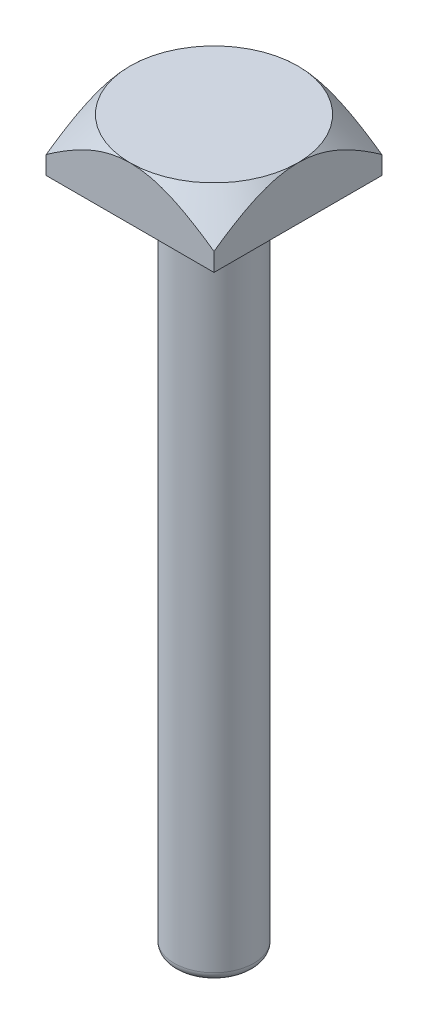
SolidWorks part; units mm, degrees
ref_plane "Front Plane" through (0, 0, 0) normal (0, 0, 1) x (1, 0, 0)
ref_plane "Top Plane" through (0, 0, 0) normal (0, 1, 0) x (1, 0, 0)
ref_plane "Right Plane" through (0, 0, 0) normal (1, 0, 0) x (0, 0, -1)
sketch "Sketch1" plane through (0, 0, 0) normal (0, 0, 1) x (1, 0, 0)
  line L1 (0, 0) -> (4.5, 0)
  line L2 (0, 0) -> (0, -76)
  line L3 (0, -76) -> (4.5, -76)
  line L4 (4.5, 0) -> (4.5, -76)
  dimension "D1" = 76
  dimension "D2" = 4.5
revolve "Revolve1" add sketch "Sketch1" angle 360 about L4
sketch "Sketch2" plane through (0, 0, 0) normal (0, 1, 0) x (1, 0, 0)
  line L1 (-5, 9.5) -> (14, 9.5)
  line L2 (-5, 9.5) -> (-5, -9.5)
  line L3 (-5, -9.5) -> (14, -9.5)
  line L4 (14, 9.5) -> (14, -9.5)
  line L5 (-5, 9.5) -> (14, -9.5) construction
  line L6 (-5, -9.5) -> (14, 9.5) construction
  point P0 (4.5, 0)
  dimension "D1" = 19
  dimension "D2" = 19
extrude "Boss-Extrude1" add sketch "Sketch2" along normal blind 6
fillet "Fillet4" radius 1 1 edges at (0, -76, 0)
sketch "Sketch7" plane through (0, 6, 0) normal (0, 1, 0) x (1, 0, 0)
  line L0 (4.5, 9.5) -> (4.5, -9.5) construction
  line L1 (14, 9.5) -> (-5, 9.5) construction
  line L2 (-5, -9.5) -> (14, -9.5) construction
  line L3 (-5, 0) -> (14, 0) construction
  line L4 (-5, 9.5) -> (-5, -9.5) construction
  line L5 (14, -9.5) -> (14, 9.5) construction
  circle A0 centre (4.5, 0) radius 9.5
  dimension "D1" = 9.5
extrude "Cut-Extrude1" cut sketch "Sketch7" against normal blind 10 draft 45 flip side to cut
